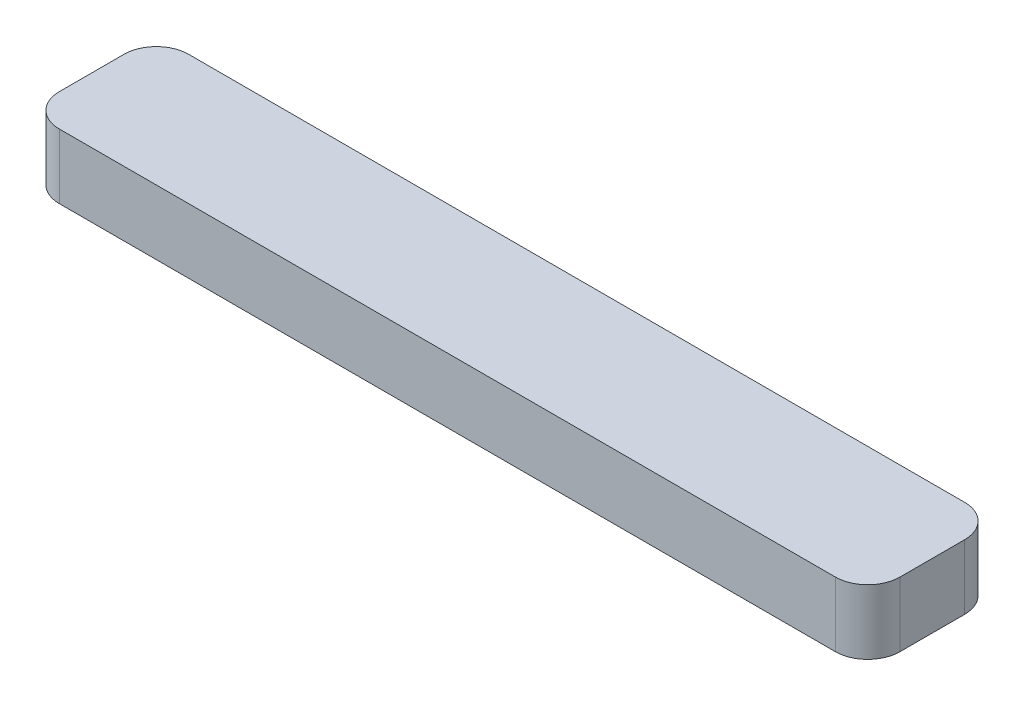
SolidWorks part; units mm, degrees
ref_plane "Front Plane" through (0, 0, 0) normal (0, 0, 1) x (1, 0, 0)
ref_plane "Top Plane" through (0, 0, 0) normal (0, 1, 0) x (1, 0, 0)
ref_plane "Right Plane" through (0, 0, 0) normal (1, 0, 0) x (0, 0, -1)
sketch "Sketch2" plane through (0, 0, 0) normal (0, 1, 0) x (1, 0, 0)
  line L1 (-6, 1) -> (6, 1)
  line L2 (-6.5, 0.5) -> (-6.5, -0.5)
  line L3 (-6, -1) -> (6, -1)
  line L4 (6.5, 0.5) -> (6.5, -0.5)
  line L5 (-6.5, 1) -> (6.5, -1) construction
  line L6 (-6.5, -1) -> (6.5, 1) construction
  arc A0 (6, -1) -> (6.5, -0.5) centre (6, -0.5) ccw
  arc A1 (6, 1) -> (6.5, 0.5) centre (6, 0.5) cw
  arc A2 (-6.5, -0.5) -> (-6, -1) centre (-6, -0.5) ccw
  arc A3 (-6, 1) -> (-6.5, 0.5) centre (-6, 0.5) ccw
  point P0 (0, 0)
  dimension "D3" = 0.5
  dimension "D1" = 13
  dimension "D2" = 2
extrude "Boss-Extrude1" add sketch "Sketch2" along normal blind 1
